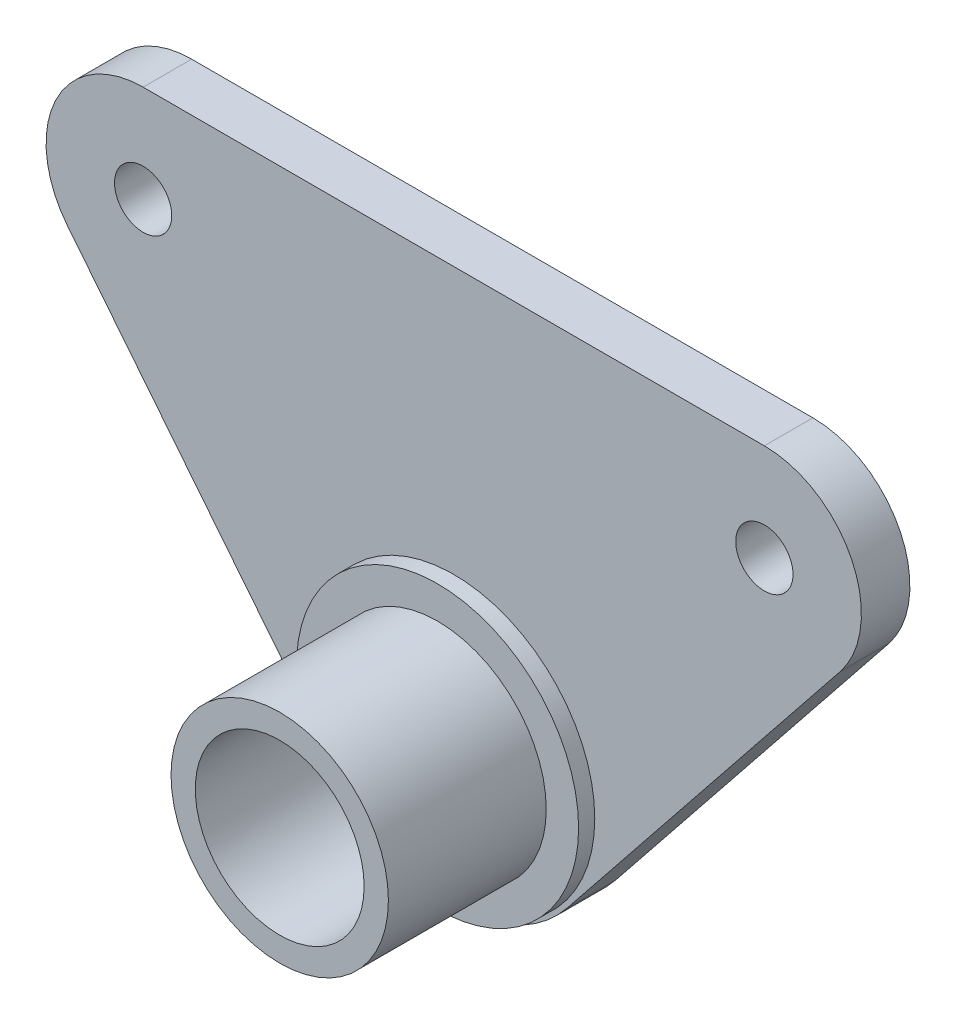
SolidWorks part; units mm, degrees
ref_plane "Front Plane" through (0, 0, 0) normal (0, 0, 1) x (1, 0, 0)
ref_plane "Top Plane" through (0, 0, 0) normal (0, 1, 0) x (1, 0, 0)
ref_plane "Right Plane" through (0, 0, 0) normal (1, 0, 0) x (0, 0, -1)
sketch "Sketch1" plane through (0, 0, 0) normal (0, 0, 1) x (1, 0, 0)
  line L0 (-24.39, 32.01) -> (24.39, 32.01)
  line L1 (-24.39, 28.2) -> (24.39, 28.2) construction
  line L2 (-28.2, 24.39) -> (-28.2, -24.39) construction
  line L3 (-24.39, -28.2) -> (24.39, -28.2) construction
  line L4 (28.2, 24.39) -> (28.2, -24.39) construction
  line L5 (-28.2, 28.2) -> (28.2, -28.2) construction
  line L6 (-28.2, -28.2) -> (28.2, 28.2) construction
  line L7 (32.01, 24.39) -> (32.01, -24.39) construction
  line L8 (-24.39, -32.01) -> (24.39, -32.01) construction
  line L9 (-32.01, 24.39) -> (-32.01, -24.39) construction
  line L10 (-23.57, 23.57) -> (0, -17.2544) construction
  line L11 (0, -17.2544) -> (23.57, 23.57) construction
  line L12 (-28.2, 23.57) -> (23.57, 23.57) construction
  line L14 (-8.9255, -7.14) -> (-30.3403, 19.63)
  line L15 (8.9255, -7.14) -> (30.3403, 19.63)
  circle A0 centre (-23.57, 23.57) radius 2.5 construction
  circle A1 centre (23.57, 23.57) radius 2.5 construction
  arc A2 (-32.01, 24.39) -> (-24.39, 32.01) centre (-24.39, 24.39) cw construction
  arc A3 (32.01, 24.39) -> (24.39, 32.01) centre (24.39, 24.39) ccw construction
  arc A4 (-28.2, 24.39) -> (-24.39, 28.2) centre (-24.39, 24.39) cw construction
  arc A5 (-28.2, -24.39) -> (-24.39, -28.2) centre (-24.39, -24.39) ccw construction
  arc A6 (28.2, -24.39) -> (24.39, -28.2) centre (24.39, -24.39) cw construction
  arc A7 (28.2, 24.39) -> (24.39, 28.2) centre (24.39, 24.39) ccw construction
  arc A8 (30.3403, 19.63) -> (24.39, 32.01) centre (24.39, 24.39) ccw
  arc A9 (32.01, -24.39) -> (24.39, -32.01) centre (24.39, -24.39) cw construction
  arc A10 (-32.01, -24.39) -> (-24.39, -32.01) centre (-24.39, -24.39) ccw construction
  arc A11 (-30.3403, 19.63) -> (-24.39, 32.01) centre (-24.39, 24.39) cw
  arc A12 (-8.9255, -7.14) -> (8.9255, -7.14) centre (0, 0) ccw
  point P0 (0, 0)
  dimension "D3" = 5
  dimension "D4" = 5
  dimension "D5" = 60
  dimension "D6" = 60
  dimension "D11" = 3.81
  dimension "D12" = 3.81
  dimension "D9" = 22.86
  dimension "D1" = 56.4
  dimension "D2" = 56.4
  dimension "D7" = 47.14
  dimension "D13" = 3.81
extrude "Boss-Extrude1" add sketch "Sketch1" along normal blind 3.81
sketch "Sketch2" plane through (0, 0, 3.81) normal (0, 0, 1) x (1, 0, 0)
  circle A0 centre (0, 0) radius 8.5344
  circle A1 centre (0, 0) radius 6.6294
  dimension "D1" = 17.0688
  dimension "D2" = 1.905
extrude "Boss-Extrude2" add sketch "Sketch2" along normal blind 17.4752 from surface at -3.81 starting at face at (0, 14.742, 0)
sketch "Sketch4" plane through (0, 0, 3.81) normal (0, 0, 1) x (1, 0, 0)
  circle A0 centre (0, 0) radius 6.6294
  circle A1 centre (0, 0) radius 6.6294 construction
extrude "Cut-Extrude2" cut sketch "Sketch4" against normal through all
sketch "Sketch5" plane through (0, 0, 3.81) normal (0, 0, 1) x (1, 0, 0)
  circle A1 centre (0, 0) radius 11.0744
  arc A2 (8.5344, 0) -> (8.5344, 0) centre (0, 0) ccw
  circle A3 centre (0, 0) radius 8.5344
  dimension "D1" = 0
  dimension "D2" = 2.54
extrude "Boss-Extrude3" add sketch "Sketch5" along normal blind 1.27 and the other way up to surface (3.81 mm away) other way up to face at (6.6294, 0, 0)
hole_wizard "#8 Clearance Hole1" positions "Sketch7" profile "Sketch6" hole size "#8" standard "ANSI Inch" end condition through all
sketch "Sketch7" plane through (0, 0, 3.81) normal (0, 0, 1) x (1, 0, 0)
  point P0 (-24.39, 24.39)
  point P3 (24.39, 24.39)
sketch "Sketch6" plane through (-24.39, 24.39, 3.81) normal (1, 0, 0) x (0, -1, 0)
  line L0 (0, 0) -> (0, 3.81)
  line L1 (0, 3.81) -> (2.2479, 3.81)
  line L2 (2.2479, 3.81) -> (2.2479, 0)
  line L5 (2.2479, 0) -> (0, 0)
  line L11 (0, -6.35) -> (0, 107.95) construction
  dimension "Thru Hole Dia." = 4.4958
  dimension "Thru Hole Depth" = 3.81
